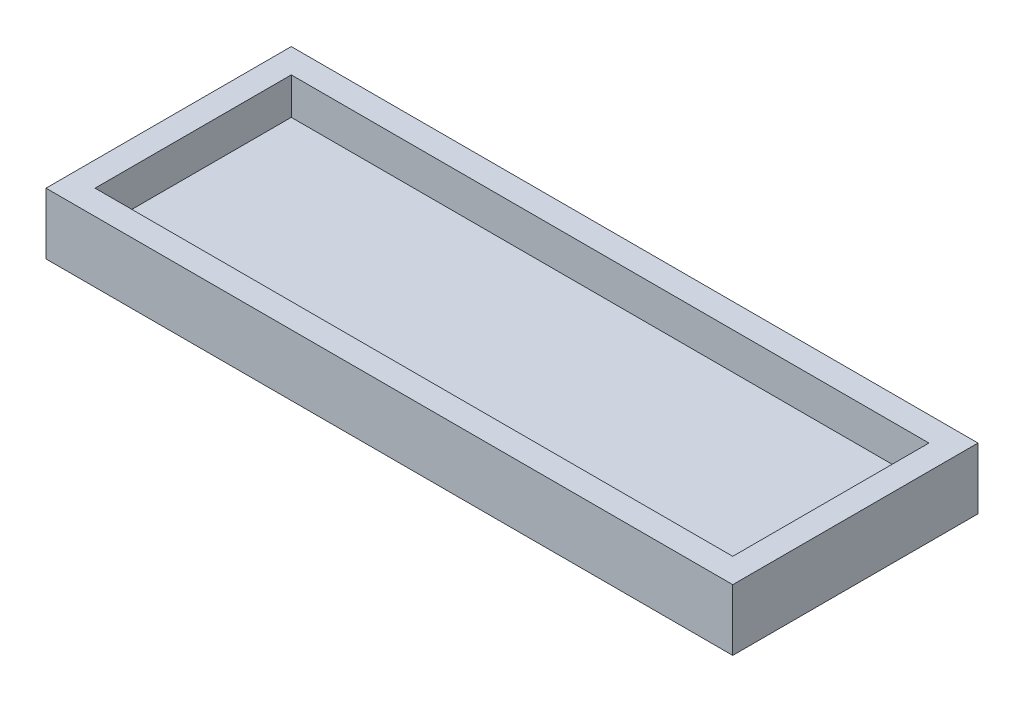
SolidWorks part; units mm, degrees
ref_plane "前视基准面" through (0, 0, 0) normal (0, 0, 1) x (1, 0, 0)
ref_plane "上视基准面" through (0, 0, 0) normal (0, 1, 0) x (1, 0, 0)
ref_plane "右视基准面" through (0, 0, 0) normal (1, 0, 0) x (0, 0, -1)
other "Configuration Table"
sketch "草图1" plane through (0, 0, 0) normal (0, 1, 0) x (1, 0, 0)
  line L1 (-13, -4) -> (13, -4)
  line L2 (-13, -4) -> (-13, 4)
  line L3 (-13, 4) -> (13, 4)
  line L4 (13, -4) -> (13, 4)
  line L5 (-13, -4) -> (13, 4) construction
  line L6 (-13, 4) -> (13, -4) construction
  point P0 (0, 0)
  dimension "D1" = 8
  dimension "D2" = 26
extrude "凸台-拉伸1" add sketch "草图1" along normal blind 1
sketch "草图2" plane through (0, 1, 0) normal (0, 1, 0) x (1, 0, 0)
  line L4 (14, -5) -> (14, 5)
  line L5 (14, 5) -> (-14, 5)
  line L6 (-14, 5) -> (-14, -5)
  line L7 (-14, -5) -> (14, -5)
  line L8 (13, -4) -> (13, 4)
  line L9 (13, 4) -> (-13, 4)
  line L10 (-13, 4) -> (-13, -4)
  line L11 (-13, -4) -> (13, -4)
  line L12 (13, -4) -> (13, 4)
  line L13 (13, 4) -> (-13, 4)
  line L14 (-13, 4) -> (-13, -4)
  line L15 (-13, -4) -> (13, -4)
  dimension "D1" = 0
  dimension "D2" = 1
extrude "凸台-拉伸2" add sketch "草图2" along normal blind 1.5 and the other way blind 1
